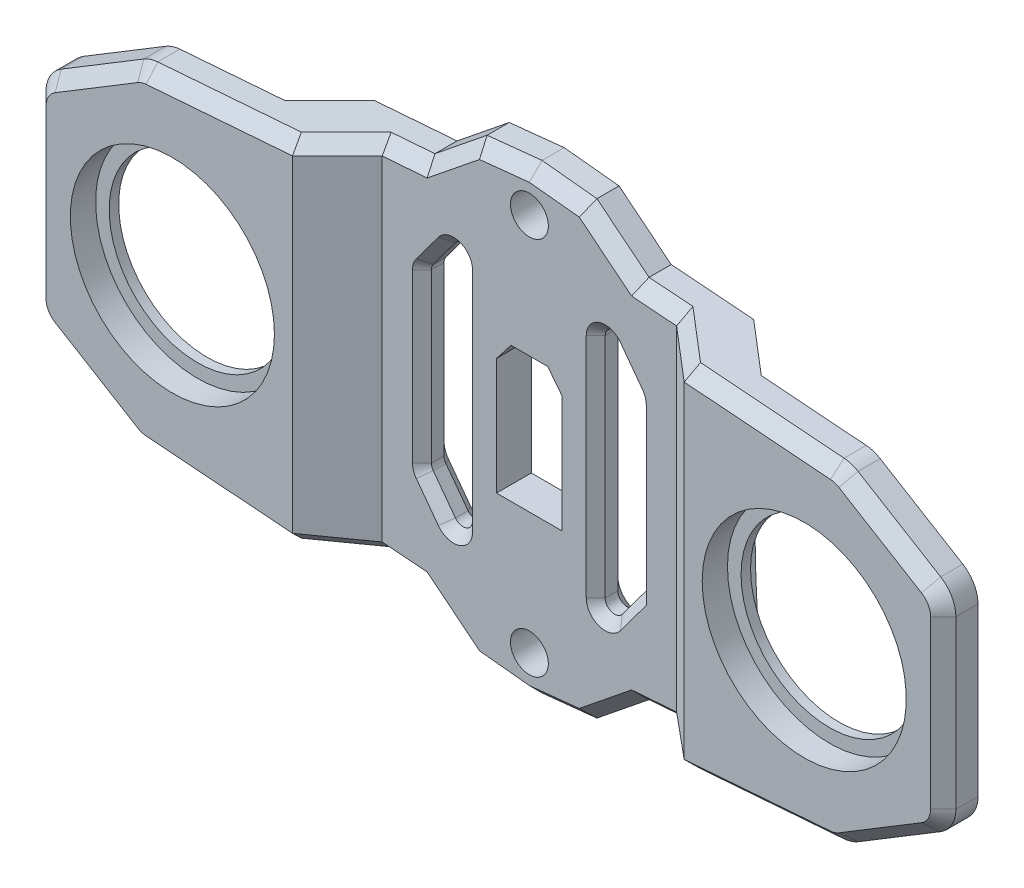
SolidWorks part; units mm, degrees
ref_plane "Front Plane" through (0, 0, 0) normal (0, 0, 1) x (1, 0, 0)
ref_plane "Top Plane" through (0, 0, 0) normal (0, 1, 0) x (1, 0, 0)
ref_plane "Right Plane" through (0, 0, 0) normal (1, 0, 0) x (0, 0, -1)
sketch "Sketch1" plane through (0, 0, 0) normal (0, 0, 1) x (1, 0, 0)
  line L0 (0, 0) -> (-50, 0) construction
  line L1 (0, 0) -> (0, 30) construction
  line L4 (-72, 16) -> (-72, -16)
  line L11 (0, 36.5) -> (-8.6898, 35.5988)
  line L12 (-8.6898, 35.5988) -> (-16.9442, 28.942)
  line L13 (-16.9442, 28.942) -> (-55.5, 26)
  line L14 (-55.5, 26) -> (-72, 16)
  line L15 (-55.5, -26) -> (-72, -16)
  line L16 (-16.9442, -28.942) -> (-55.5, -26)
  line L17 (-8.6898, -35.5988) -> (-16.9442, -28.942)
  line L18 (0, -36.5) -> (-8.6898, -35.5988)
  line L20 (0, -36.5) -> (8.6898, -35.5988)
  line L21 (8.6898, -35.5988) -> (16.9442, -28.942)
  line L22 (16.9442, -28.942) -> (55.5, -26)
  line L23 (55.5, -26) -> (72, -16)
  line L24 (55.5, 26) -> (72, 16)
  line L25 (16.9442, 28.942) -> (55.5, 26)
  line L26 (8.6898, 35.5988) -> (16.9442, 28.942)
  line L27 (0, 36.5) -> (8.6898, 35.5988)
  line L28 (72, 16) -> (72, -16)
  circle A0 centre (0, 30) radius 3
  circle A1 centre (-50, 0) radius 16.15
  circle A2 centre (0, -30) radius 3
  circle A4 centre (50, 0) radius 16.15
  point P13 (-72, 0)
  point P18 (72, 0)
  point P22 (0, -36.5)
  dimension "D1" = 6
  dimension "D3" = 32.3
  dimension "D2" = 50
  dimension "D4" = 60
  dimension "D5" = 72
  dimension "D6" = 73
  dimension "D7" = 52
  dimension "D8" = 32
  dimension "D9" = 16.5
extrude "Boss-Extrude1" add sketch "Sketch1" along normal blind 12
sketch "Sketch2" plane through (0, 0, 0) normal (0, 1, 0) x (1, 0, 0)
  line L0 (-31, -12) -> (-23.3, -5.5)
  line L2 (-23.3, -5.5) -> (4.3946, -5.5)
  line L3 (-31, -12) -> (31, -12)
  line L5 (0, 20.7446) -> (0, -29.3903) construction
  line L6 (-72, 0) -> (-72, -6.5)
  line L8 (-72, -6.5) -> (-37.7, -6.5)
  line L9 (-37.7, -6.5) -> (-30, 0)
  line L10 (-30, 0) -> (-72, 0)
  line L11 (30, 0) -> (72, 0)
  line L12 (37.7, -6.5) -> (30, 0)
  line L13 (72, -6.5) -> (37.7, -6.5)
  line L14 (72, 0) -> (72, -6.5)
  line L15 (23.3, -5.5) -> (4.3946, -5.5)
  line L16 (31, -12) -> (23.3, -5.5)
  line L18 (-72, -12) -> (-72, 0) construction
  line L19 (-55.5, -12) -> (-72, -12) construction
  line L20 (-8.6898, 0) -> (-16.9442, 0) construction
  line L21 (-16.9442, -12) -> (-55.5, -12) construction
  point P25 (0, -12)
  dimension "D1" = 62
  dimension "D2" = 5.5
  dimension "D3" = 5.5
  dimension "D4" = 7.7
  dimension "D5" = 42
extrude "Cut-Extrude1" cut sketch "Sketch2" against normal through all both and the other way through all
sketch "Sketch3" plane through (0, 0, 5.5) normal (0, 0, 1) x (1, 0, 0)
  line L0 (5.2, -10.7) -> (-5.2, -10.7)
  line L1 (-5, 10.5) -> (5, 10.5) construction
  line L2 (-5, 10.5) -> (-5, -10.5) construction
  line L3 (-5, -10.5) -> (5, -10.5) construction
  line L4 (5, 10.5) -> (5, -10.5) construction
  line L5 (-5, 10.5) -> (5, -10.5) construction
  line L6 (-5, -10.5) -> (5, 10.5) construction
  line L7 (-5.2, -10.7) -> (-5.2, 7.758)
  line L8 (-5.2, 7.758) -> (-2.9087, 10.7)
  line L9 (-2.9087, 10.7) -> (2.9087, 10.7)
  line L10 (0, 14.3964) -> (0, -14.2533) construction
  line L11 (5.2, -10.7) -> (5.2, 7.758)
  line L12 (5.2, 7.758) -> (2.9087, 10.7)
  point P0 (0, 0)
  point P15 (0, -10.7)
  point P17 (0, 10.7)
  dimension "D1" = 0.2
  dimension "D2" = 0.2
  dimension "D3" = 0.2
  dimension "D4" = 21
  dimension "D5" = 10
extrude "Cut-Extrude2" cut sketch "Sketch3" against normal through all both and the other way through all
sketch "Sketch4" plane through (0, 0, 5.5) normal (0, 0, 1) x (1, 0, 0)
  line L0 (-17, 13.75) -> (-17, -13.75)
  line L1 (-17, -13.75) -> (-10.5, -22.5)
  line L2 (-10.5, -22.5) -> (-10.5, 22.5)
  line L3 (-25.9785, 0) -> (17.2443, 0) construction
  line L4 (0, 18.6228) -> (0, -13.7834) construction
  line L5 (-17, 13.75) -> (-10.5, 22.5)
  line L6 (17, 13.75) -> (10.5, 22.5)
  line L7 (10.5, -22.5) -> (10.5, 22.5)
  line L8 (17, -13.75) -> (10.5, -22.5)
  line L9 (17, 13.75) -> (17, -13.75)
  point P0 (17, 0)
  point P10 (-10.5, 0)
  point P11 (-17, 0)
  point P12 (10.5, 0)
  dimension "D1" = 6.5
  dimension "D2" = 45
  dimension "D3" = 27.5
  dimension "D4" = 10.5
extrude "Cut-Extrude3" cut sketch "Sketch4" against normal through all both and the other way through all
fillet "Fillet1" radius 1.5 7 edges at (17, 13.75, 2.75) (10.5, 22.5, 2.75) (10.5, -22.5, 2.75) (-10.5, -22.5, 2.75) (-17, -13.75, 2.75) (-17, 13.75, 2.75) (-10.5, 22.5, 2.75)
sketch "Sketch5" plane through (0, 0, 6.5) normal (0, 0, 1) x (1, 0, 0)
  line L0 (0, 45.7061) -> (0, -41.975) construction
  circle A0 centre (-50, 0) radius 14
  circle A1 centre (-50, 0) radius 18.0732
  circle A2 centre (50, 0) radius 18.0732
  circle A3 centre (50, 0) radius 14
  dimension "D1" = 28
extrude "Boss-Extrude2" add sketch "Sketch5" along normal blind 1.5
fillet "Fillet2" radius 5 8 edges at (72, -16, 9.25) (72, 16, 9.25) (-72, -16, 9.25) (-72, 16, 9.25) (55.5, 26, 9.25) (55.5, -26, 9.25) (-55.5, -26, 9.25) (-55.5, 26, 9.25)
chamfer "Chamfer1" distance 2 angle 45 34 edges at (-27.15, 28.1633, 8.75) (-20.1221, 28.6995, 5.5) (-12.817, 32.2704, 5.5) (-4.3449, 36.0494, 5.5) (4.3449, 36.0494, 5.5) (12.817, 32.2704, 5.5) (20.1221, 28.6995, 5.5) (27.15, 28.1633, 8.75) (42.6549, 26.9802, 12) (63.0562, 21.4205, 12) (72, 0, 12) (63.0562, -21.4205, 12) (42.6549, -26.9802, 12) (27.15, -28.1633, 8.75) (20.1221, -28.6995, 5.5) (12.817, -32.2704, 5.5) (4.3449, -36.0494, 5.5) (-4.3449, -36.0494, 5.5) (-12.817, -32.2704, 5.5) (-20.1221, -28.6995, 5.5) (-27.15, -28.1633, 8.75) (-42.6549, -26.9802, 12) (-63.0562, -21.4205, 12) (-72, 0, 12) (-63.0562, 21.4205, 12) (-42.6549, 26.9802, 12) (71.3565, 15.6375, 12) (71.3565, -15.6375, 12) (-71.3565, -15.6375, 12) (-71.3565, 15.6375, 12) (55.4571, 25.8662, 12) (55.4571, -25.8662, 12) (-55.4571, -25.8662, 12) (-55.4571, 25.8662, 12)
sketch "Sketch7" plane through (0, 0, 6.5) normal (0, 0, -1) x (-1, 0, 0)
  circle A0 centre (-50, 0) radius 18.5
  circle A1 centre (50, 0) radius 18.5
  dimension "D1" = 37
extrude "Cut-Extrude4" cut sketch "Sketch7" along normal through all
chamfer "Chamfer2" distance 2 angle 45 15 edges at (-17, 0, 0) (-16.9241, -13.7249, 0) (-16.9241, 13.7249, 0) (-14.9541, -16.5041, 0) (-14.9541, 16.5041, 0) (-11.5289, -19.3895, 0) (-11.5289, 19.3895, 0) (-10.5, 0, 0) (15.1021, -16.3049, 0) (11.5289, -19.3895, 0) (10.5, 0, 0) (11.5289, 19.3895, 0) (14.9541, 16.5041, 0) (16.9241, 13.7249, 0) (17, -0.2481, 0)
chamfer "Chamfer3" distance 1.5 angle 45 15 edges at (-17, 0, 5.5) (-16.9241, 13.7249, 5.5) (-16.9241, -13.7249, 5.5) (-14.9541, 16.5041, 5.5) (-14.9541, -16.5041, 5.5) (-11.5289, 19.3895, 5.5) (-11.5289, -19.3895, 5.5) (-10.5, 0, 5.5) (17, -0.2481, 5.5) (16.9241, 13.7249, 5.5) (15.1021, -16.3049, 5.5) (14.9541, 16.5041, 5.5) (11.5289, -19.3895, 5.5) (11.5289, 19.3895, 5.5) (10.5, 0, 5.5)
